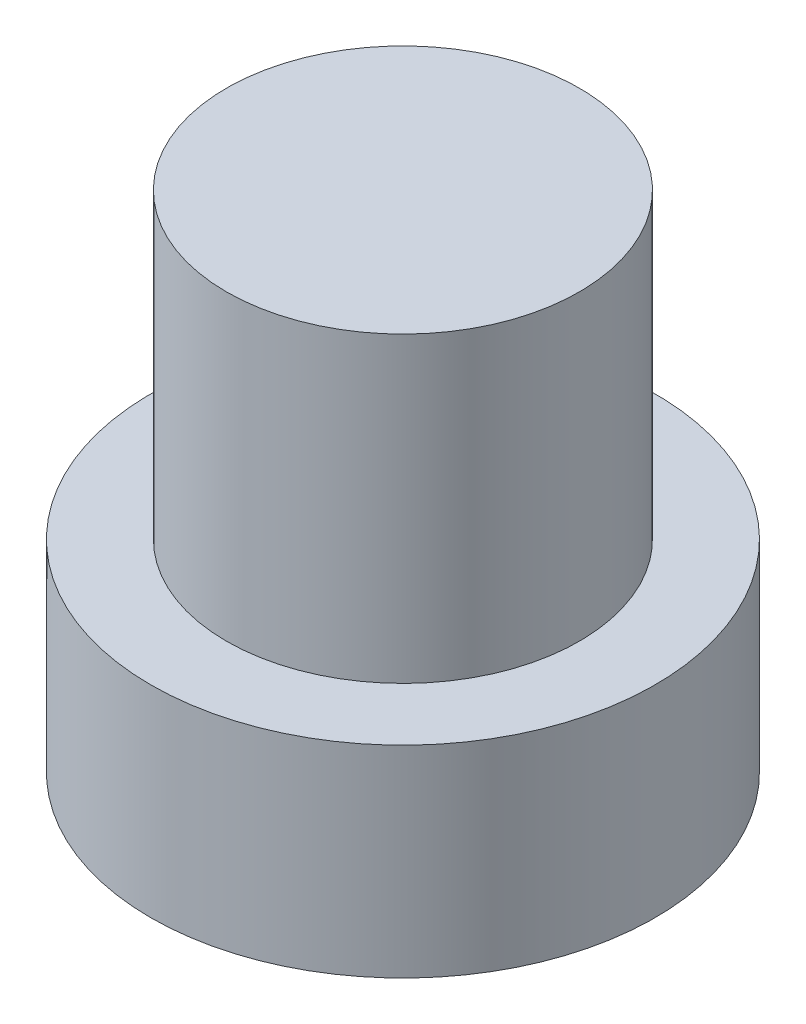
SolidWorks part; units mm, degrees
ref_plane "Front Plane" through (0, 0, 0) normal (0, 0, 1) x (1, 0, 0)
ref_plane "Top Plane" through (0, 0, 0) normal (0, 1, 0) x (1, 0, 0)
ref_plane "Right Plane" through (0, 0, 0) normal (1, 0, 0) x (0, 0, -1)
sketch "Sketch1" plane through (0, 0, 0) normal (0, 1, 0) x (1, 0, 0)
  circle A0 centre (0, 0) radius 5
  dimension "D1" = 10
extrude "Boss-Extrude1" add sketch "Sketch1" along normal blind 4
sketch "Sketch2" plane through (0, 4, 0) normal (0, 1, 0) x (1, 0, 0)
  circle A0 centre (0, 0) radius 3.5
  dimension "D1" = 7
extrude "Boss-Extrude2" add sketch "Sketch2" along normal blind 6
